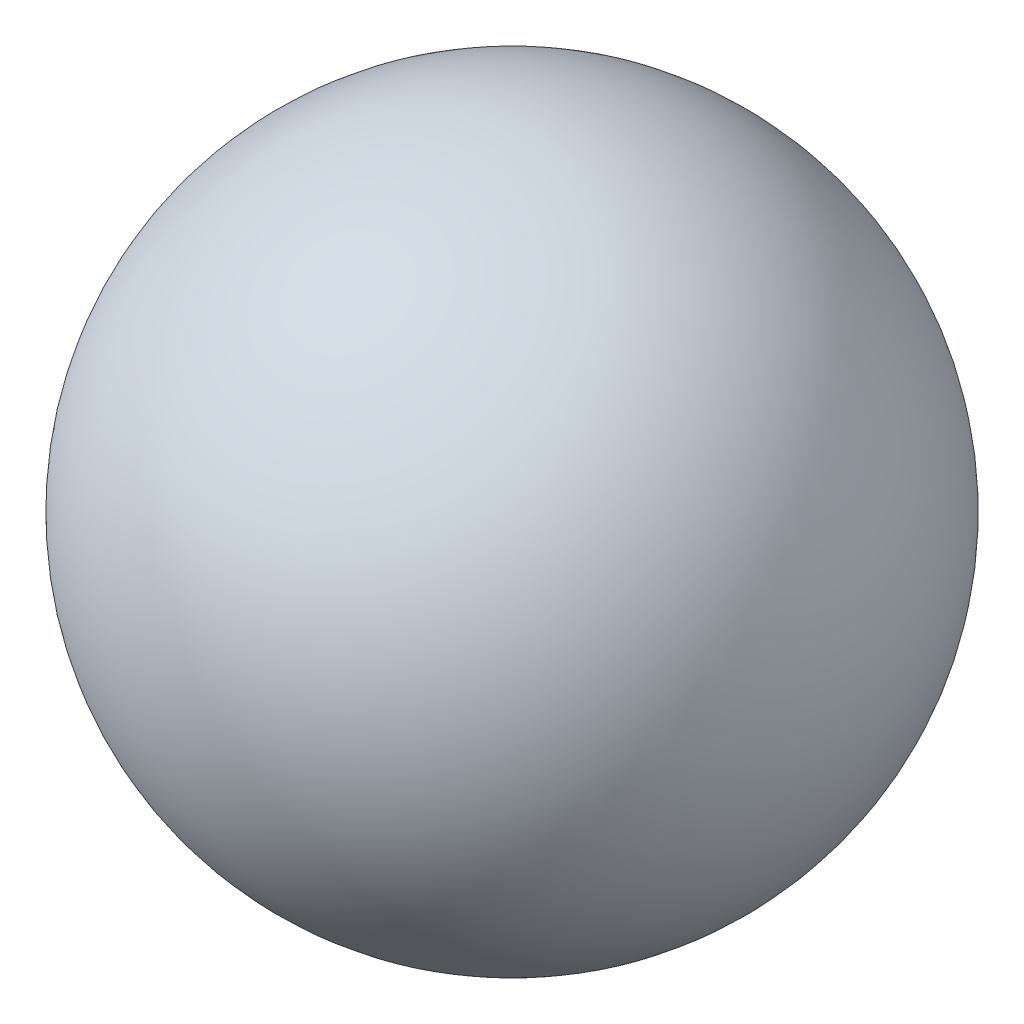
SolidWorks part; units mm, degrees
ref_plane "Front Plane" through (0, 0, 0) normal (0, 0, 1) x (1, 0, 0)
ref_plane "Top Plane" through (0, 0, 0) normal (0, 1, 0) x (1, 0, 0)
ref_plane "Right Plane" through (0, 0, 0) normal (1, 0, 0) x (0, 0, -1)
sketch "Sketch1" plane through (0, 0, 0) normal (0, 0, 1) x (1, 0, 0)
  line L0 (0, 9.4781) -> (0, -9.6892) construction
  line L1 (0, 4) -> (0, -4)
  arc A0 (0, -4) -> (0, 4) centre (0, 0) ccw
  dimension "D1" = 8
revolve "Revolve1" add sketch "Sketch1" angle 360 about L0
